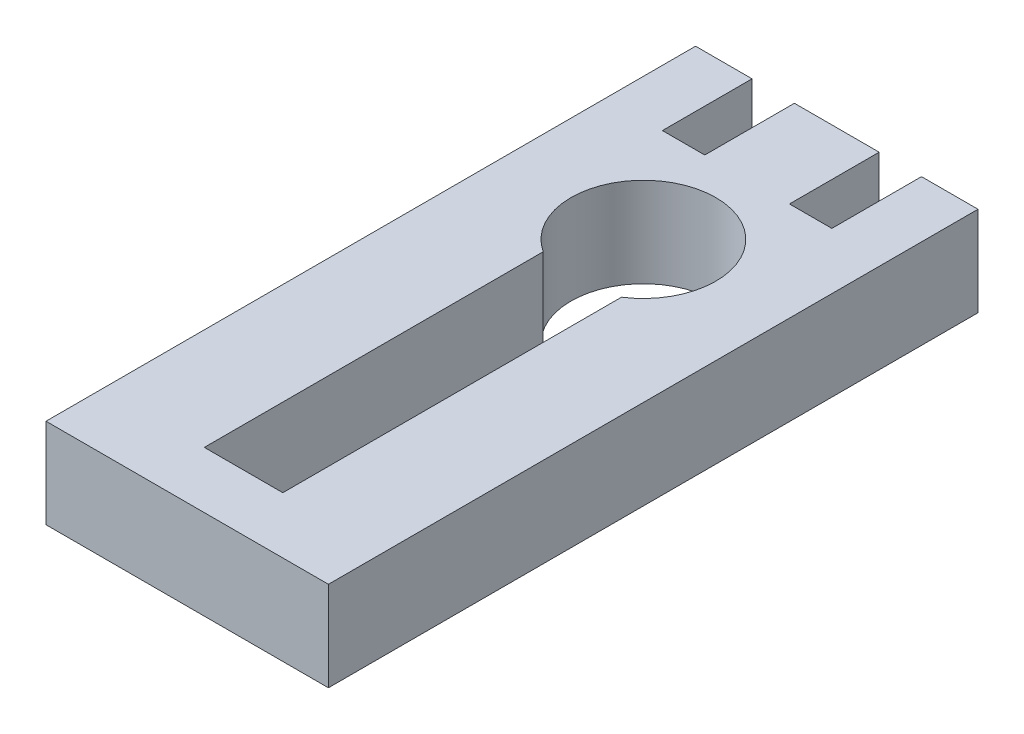
SolidWorks part; units mm, degrees
ref_plane "Front Plane" through (0, 0, 0) normal (0, 0, 1) x (1, 0, 0)
ref_plane "Top Plane" through (0, 0, 0) normal (0, 1, 0) x (1, 0, 0)
ref_plane "Right Plane" through (0, 0, 0) normal (1, 0, 0) x (0, 0, -1)
sketch "Sketch1" plane through (0, 0, 0) normal (0, 1, 0) x (1, 0, 0)
  line L1 (0, 0) -> (10, 0)
  line L2 (0, 0) -> (0, 23)
  line L3 (0, 23) -> (2, 23)
  line L4 (10, 0) -> (10, 23)
  line L7 (2, 23) -> (2, 19.825)
  line L8 (2, 19.825) -> (3.5, 19.825)
  line L9 (3.5, 23) -> (3.5, 19.825)
  line L14 (5, 0) -> (5, 23.6636) construction
  line L16 (3.5, 23) -> (6.5, 23)
  line L17 (6.5, 23) -> (6.5, 19.825)
  line L18 (8, 19.825) -> (6.5, 19.825)
  line L19 (8, 23) -> (8, 19.825)
  line L20 (10, 23) -> (8, 23)
  point P13 (5, 23)
  dimension "D1" = 23
  dimension "D2" = 10
  dimension "D3" = 1.5
  dimension "D4" = 1.5
  dimension "D6" = 3.175
extrude "Boss-Extrude1" add sketch "Sketch1" along normal blind 3.175
sketch "Sketch3" plane through (0, 3.175, 0) normal (0, 1, 0) x (1, 0, 0)
  line L0 (0, 0) -> (10, 0) construction
  line L1 (5, 0) -> (5, 50.9927) construction
  line L5 (5, 1.435) -> (5, 50.9927) construction
  line L6 (0, 13.3286) -> (10, 13.3286) construction
  line L8 (0, 23) -> (0, 0) construction
  line L9 (10, 0) -> (10, 23) construction
  line L10 (3.605, 2) -> (6.385, 2)
  line L11 (3.605, 14) -> (3.605, 2)
  line L12 (6.385, 13.9936) -> (6.385, 2)
  arc A1 (3.605, 14) -> (6.385, 13.9936) centre (5, 16.1525) cw
  dimension "D1" = 14.1525
  dimension "D2" = 2.565
  dimension "D3" = 2
  dimension "D4" = 2.78
  dimension "D5" = 12
extrude "Cut-Extrude1" cut sketch "Sketch3" against normal up to next
